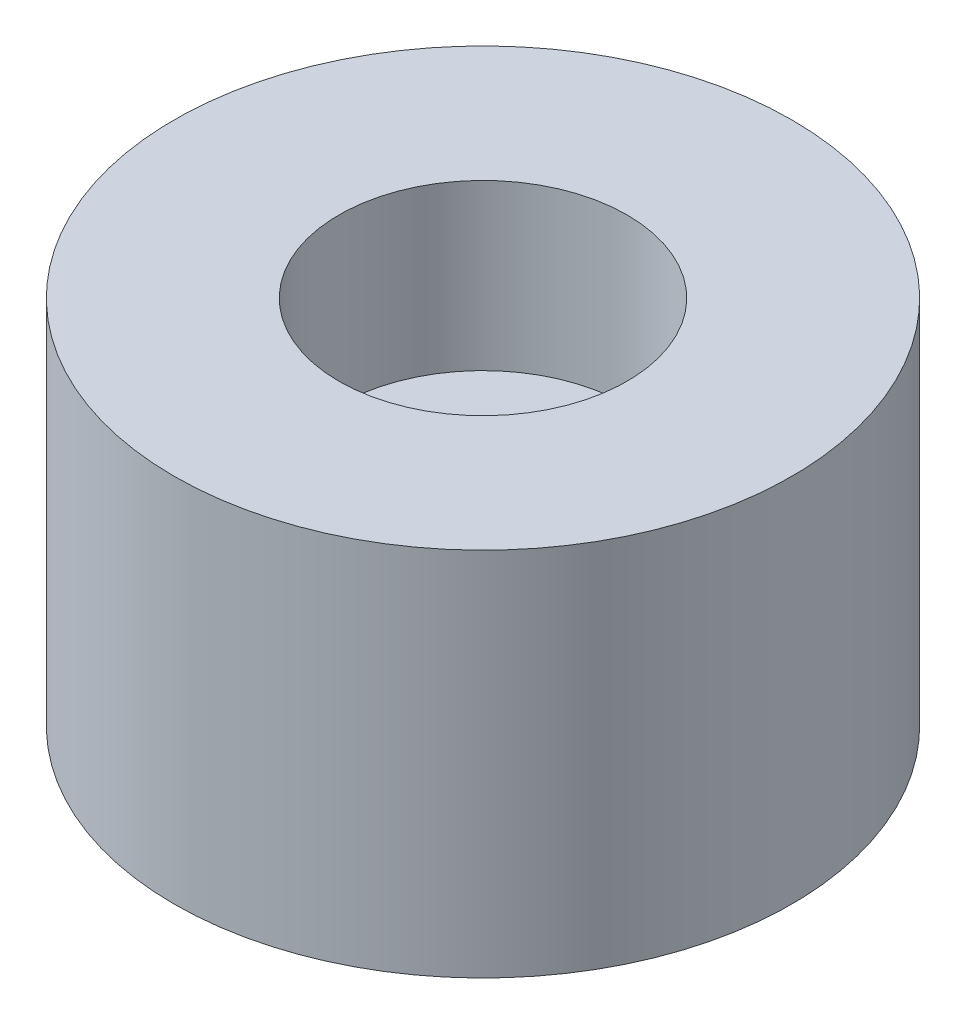
SolidWorks part; units mm, degrees
material "ABS"
ref_plane "Front Plane" through (0, 0, 0) normal (0, 0, 1) x (1, 0, 0)
ref_plane "Top Plane" through (0, 0, 0) normal (0, 1, 0) x (1, 0, 0)
ref_plane "Right Plane" through (0, 0, 0) normal (1, 0, 0) x (0, 0, -1)
sketch "Sketch1" plane through (0, 0, 0) normal (0, 0, 1) x (1, 0, 0)
  line L0 (0, 0) -> (0, 9) construction
  line L1 (0, 9) -> (3.5, 9) construction
  line L2 (3.5, 9) -> (3.5, 5)
  line L3 (3.5, 5) -> (1.75, 5)
  line L4 (1.75, 5) -> (1.75, 0)
  line L5 (1.75, 0) -> (0, 0) construction
  line L6 (1.75, 0) -> (7.5, 0)
  line L7 (7.5, 0) -> (7.5, 9)
  line L8 (7.5, 9) -> (3.5, 9)
  dimension "D1" = 3.5
  dimension "D2" = 7
  dimension "D3" = 5
  dimension "D4" = 4
  dimension "D5" = 15
revolve "Revolve1" add sketch "Sketch1" angle 360 about L0
